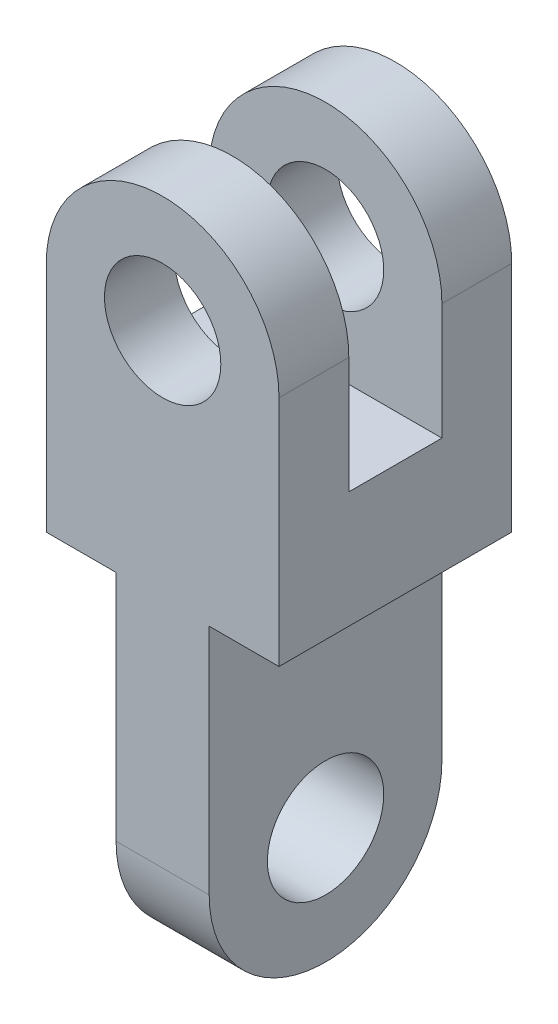
SolidWorks part; units mm, degrees
ref_plane "Alzado" through (0, 0, 0) normal (0, 0, 1) x (1, 0, 0)
ref_plane "Planta" through (0, 0, 0) normal (0, 1, 0) x (1, 0, 0)
ref_plane "Vista lateral" through (0, 0, 0) normal (1, 0, 0) x (0, 0, -1)
sketch "Croquis2" plane through (0, 0, 0) normal (0, 0, 1) x (1, 0, 0)
  line L0 (0, 0) -> (40, 0)
  line L1 (40, 0) -> (40, 150)
  line L2 (40, 150) -> (70, 150)
  line L3 (70, 150) -> (70, 250)
  line L4 (-30, 250) -> (-30, 150)
  line L5 (-30, 150) -> (0, 150)
  line L6 (0, 150) -> (0, 0)
  arc A1 (-30, 250) -> (70, 250) centre (20, 250) cw
  circle A2 centre (20, 250) radius 25
  dimension "D7" = 50
  dimension "D1" = 40
  dimension "D2" = 30
  dimension "D3" = 150
  dimension "D4" = 150
  dimension "D5" = 30
  dimension "D6" = 100
extrude "Saliente-Extruir1" add sketch "Croquis2" along normal blind 100
sketch "Croquis3" plane through (40, 0, 0) normal (1, 0, 0) x (0, 0, -1)
  line L0 (-100, 0) -> (0, 0) construction
  line L1 (0, 0) -> (0, 150) construction
  line L3 (-100, 50) -> (-100, 0)
  line L4 (-100, 0) -> (0, 0)
  line L5 (0, 0) -> (0, 50)
  arc A0 (-100, 50) -> (0, 50) centre (-50, 50) ccw
  line M3 (0, 0) -> (0, 150)
  line M5 (-100, 150) -> (-100, 0)
  line M6 (-100, 0) -> (0, 0)
  dimension "D1" = 100
extrude "Cortar-Extruir1" cut sketch "Croquis3" against normal blind 100 contours A0 M5 M6 | A0 L4 M3
sketch "Croquis4" plane through (40, 0, 0) normal (1, 0, 0) x (0, 0, -1)
  circle A0 centre (-50, 50) radius 25
  dimension "D1" = 50
extrude "Cortar-Extruir2" cut sketch "Croquis4" against normal blind 100
sketch "Croquis5" plane through (70, 0, 0) normal (1, 0, 0) x (0, 0, -1)
  line L0 (0, 150) -> (0, 300)
  line L2 (-100, 300) -> (-100, 150)
  line L3 (-100, 150) -> (0, 150)
  line L4 (0, 300) -> (-30, 300)
  line L5 (-30, 300) -> (-30, 200)
  line L6 (-30, 200) -> (-70, 200)
  line L7 (-70, 200) -> (-70, 300)
  line L8 (0, 300) -> (-100, 300) construction
  line L9 (-70, 300) -> (-100, 300)
  line L10 (-70, 300) -> (-30, 300)
  line M10 (0, 250) -> (-100, 250)
  dimension "D1" = 30
  dimension "D2" = 30
  dimension "D3" = 100
extrude "Cortar-Extruir3" cut sketch "Croquis5" against normal through all contours L10 L7 L5 M10 | L7 L6 L5 M10
equation "\"A\" = 100mm"
equation "\"B\" = 150mm"
equation "\"D4@Croquis2\"=\"B\""
equation "\"D3@Croquis2\"=\"B\""
equation "\"D6@Croquis2\"=\"A\""
